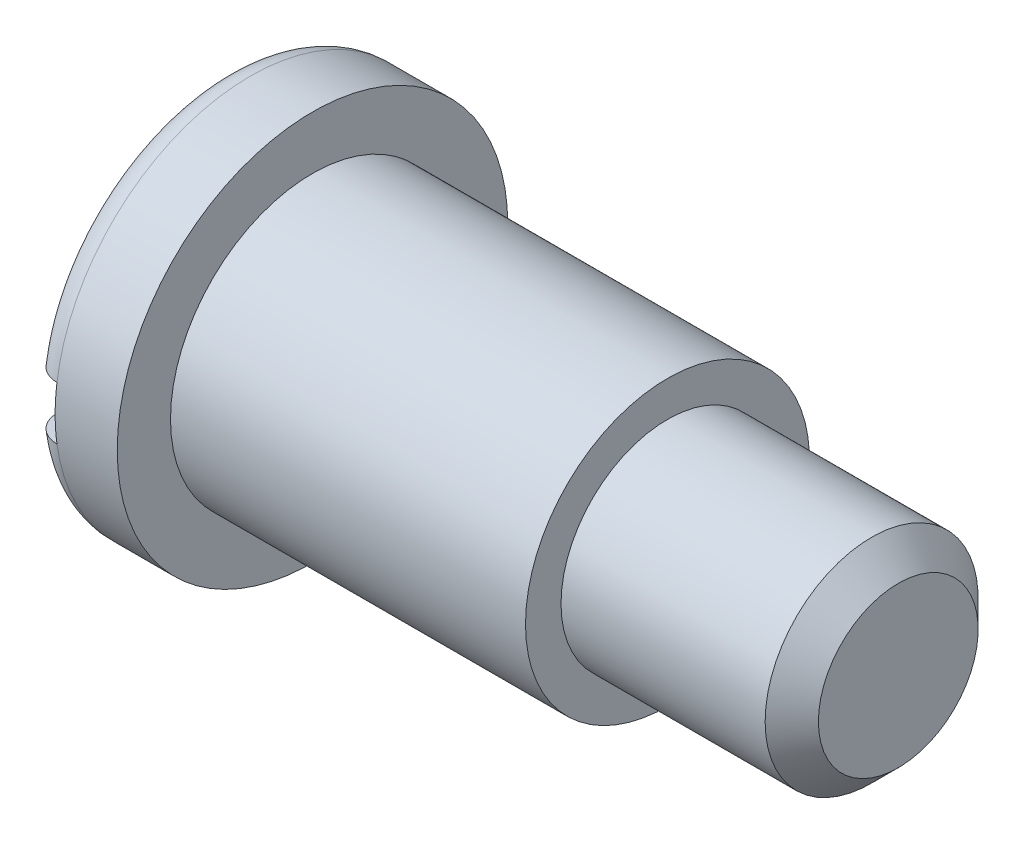
SolidWorks part; units mm, degrees
material "Stainless Steel (ferritic)"
ref_plane "Front" through (0, 0, 0) normal (0, 0, 1) x (1, 0, 0)
ref_plane "Top" through (0, 0, 0) normal (0, 1, 0) x (1, 0, 0)
ref_plane "Right" through (0, 0, 0) normal (1, 0, 0) x (0, 0, -1)
sketch "Sketch1" plane through (0, 0, 0) normal (0, 0, 1) x (1, 0, 0)
  line L0 (0, 74.2396) -> (0, -69.4185) construction
  line L1 (-97.3189, 0) -> (120.4396, 0) construction
  line L2 (0, 0) -> (0, 11)
  line L3 (0, 11) -> (5, 11)
  line L4 (5, 11) -> (5, 8)
  line L5 (5, 8) -> (25, 8)
  line L6 (25, 8) -> (25, 6)
  line L7 (25, 6) -> (38, 6)
  line L8 (38, 6) -> (38, 0)
  line L9 (38, 0) -> (0, 0)
  dimension "D1" = 38
  dimension "D2" = 20
  dimension "D3" = 5
  dimension "D4" = 22
  dimension "D5" = 16
  dimension "D6" = 12
revolve "Revolve1" add sketch "Sketch1" angle 360 about L1
cosmetic thread "Cosmetic Thread3" parameters "D2"=2.439
chamfer "Chamfer1" distance 1.5 angle 45 1 edges at (38, 0, 6)
fillet "Fillet1" radius 1.5 1 edges at (0, 0, 11)
sketch "Sketch3" plane through (0, 0, 0) normal (-1, 0, 0) x (0, 0, 1)
  line L1 (-11.8839, 1.5) -> (11.8839, 1.5)
  line L2 (-11.8839, 1.5) -> (-11.8839, -1.5)
  line L3 (-11.8839, -1.5) -> (11.8839, -1.5)
  line L4 (11.8839, 1.5) -> (11.8839, -1.5)
  line L5 (-11.8839, 1.5) -> (11.8839, -1.5) construction
  line L6 (-11.8839, -1.5) -> (11.8839, 1.5) construction
  point P0 (0, 0)
  dimension "D1" = 3
extrude "Cut-Extrude1" cut sketch "Sketch3" against normal blind 1.5
